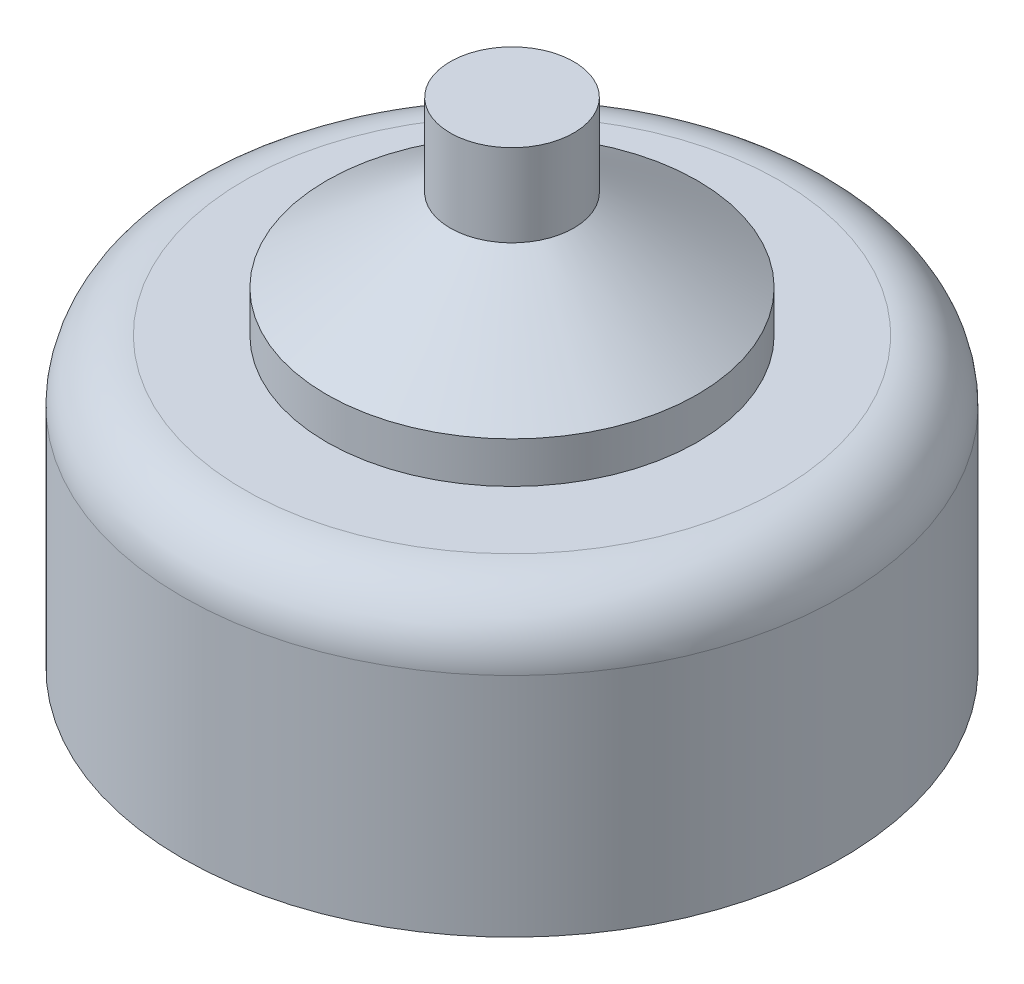
SolidWorks part; units mm, degrees
ref_plane "Front Plane" through (0, 0, 0) normal (0, 0, 1) x (1, 0, 0)
ref_plane "Top Plane" through (0, 0, 0) normal (0, 1, 0) x (1, 0, 0)
ref_plane "Right Plane" through (0, 0, 0) normal (1, 0, 0) x (0, 0, -1)
sketch "Sketch2" plane through (0, 0, 0) normal (0, 0, 1) x (1, 0, 0)
  line L0 (0, 46.0762) -> (0, -20.015) construction
  line L1 (0, -30.015) -> (8, -30.015)
  line L3 (8, -23.015) -> (4.5, -23.015)
  line L4 (4.5, -23.015) -> (4.5, -22.015)
  line L5 (4.5, -22.015) -> (1.5, -20.015)
  line L11 (8, -23.015) -> (8, -30.015)
  line L12 (1.5, -20.015) -> (1.5, -18.015)
  line L13 (1.5, -18.015) -> (0, -18.015)
  line L14 (0, -18.015) -> (0, -30.015)
  dimension "D1" = 10
  dimension "D2" = 7
revolve "Revolve1" add sketch "Sketch2" angle 360 about L0
fillet "Fillet2" radius 1.5 1 edges at (0, -23.015, 8)
